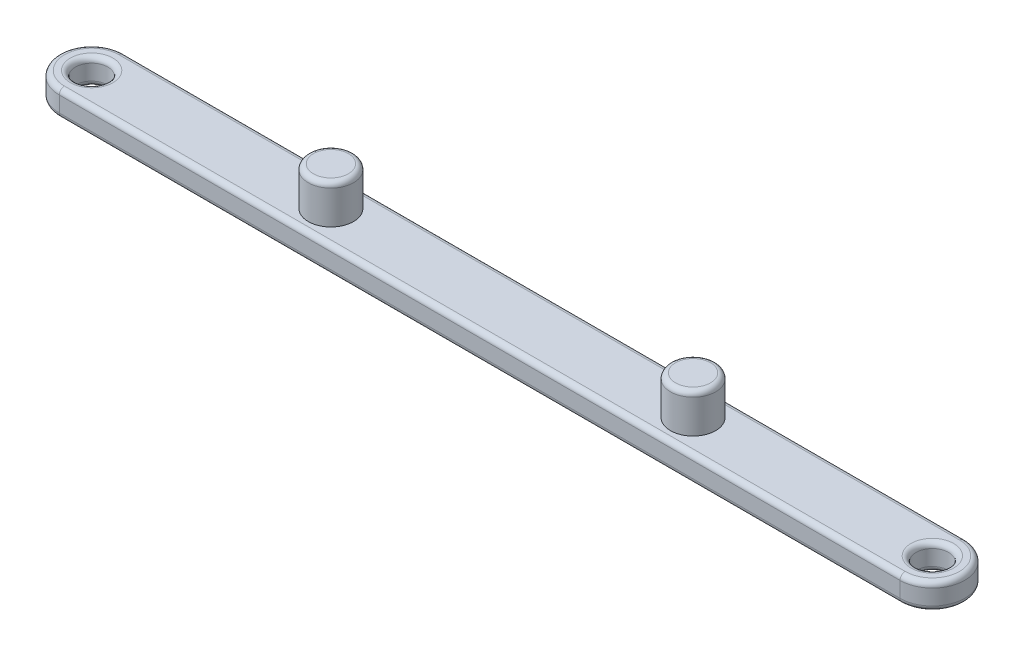
SolidWorks part; units mm, degrees
ref_plane "前视基准面" through (0, 0, 0) normal (0, 0, 1) x (1, 0, 0)
ref_plane "上视基准面" through (0, 0, 0) normal (0, 1, 0) x (1, 0, 0)
ref_plane "右视基准面" through (0, 0, 0) normal (1, 0, 0) x (0, 0, -1)
other "Configuration Table"
sketch "草图1" plane through (0, 0, 0) normal (0, 1, 0) x (1, 0, 0)
  line L0 (-32.5, 0) -> (32.5, 0) construction
  line L1 (-32.5, 2.5) -> (32.5, 2.5)
  line L2 (-32.5, -2.5) -> (32.5, -2.5)
  arc A2 (-32.5, 2.5) -> (-32.5, -2.5) centre (-32.5, 0) ccw
  arc A3 (32.5, -2.5) -> (32.5, 2.5) centre (32.5, 0) ccw
  circle A4 centre (-32.5, 0) radius 1.25
  circle A5 centre (32.5, 0) radius 1.25
  point P3 (0, 0)
  dimension "D1" = 65
  dimension "D2" = 5
  dimension "D3" = 2.5
extrude "凸台-拉伸1" add sketch "草图1" along normal blind 2
sketch "草图2" plane through (0, 2, 0) normal (0, 1, 0) x (1, 0, 0)
  circle A0 centre (14, 0) radius 1.75 construction
  circle A1 centre (-14, 0) radius 1.75 construction
  circle A2 centre (14, 0) radius 1.75
  circle A3 centre (-14, 0) radius 1.75
extrude "凸台-拉伸2" add sketch "草图2" along normal blind 3
fillet "圆角1" radius 0.4 14 edges at (14, 5, 1.75) (-14, 5, 1.75) (32.5, 0, 1.25) (-32.5, 0, 1.25) (0, 0, 2.5) (35, 0, 0) (0, 0, -2.5) (-35, 0, 0) (-35, 2, 0) (0, 2, -2.5) (35, 2, 0) (-32.5, 2, 1.25) (32.5, 2, 1.25) (0, 2, 2.5)
